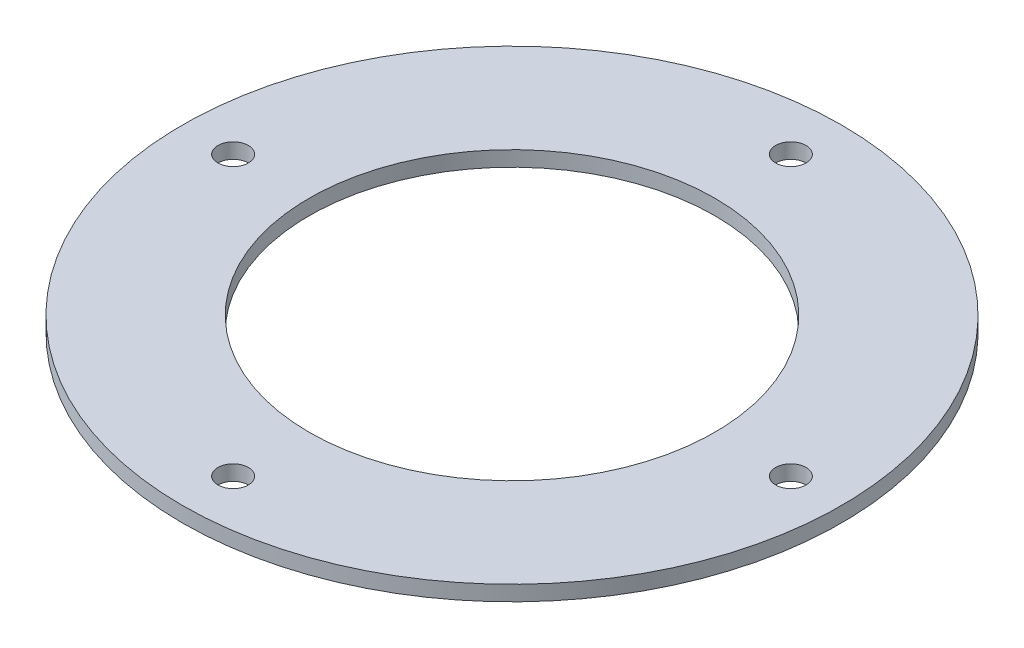
SolidWorks part; units mm, degrees
ref_plane "Front Plane" through (0, 0, 0) normal (0, 0, 1) x (1, 0, 0)
ref_plane "Top Plane" through (0, 0, 0) normal (0, 1, 0) x (1, 0, 0)
ref_plane "Right Plane" through (0, 0, 0) normal (1, 0, 0) x (0, 0, -1)
sketch "Sketch1" plane through (0, 0, 0) normal (0, 1, 0) x (1, 0, 0)
  circle A0 centre (0, 0) radius 65
  dimension "D1" = 130
extrude "Boss-Extrude1" add sketch "Sketch1" along normal blind 3
sketch "Sketch2" plane through (0, 3, 0) normal (0, 1, 0) x (1, 0, 0)
  circle A0 centre (0, 0) radius 55 construction
  circle A1 centre (0, 55) radius 3
  dimension "D1" = 110
  dimension "D2" = 6
extrude "Cut-Extrude1" cut sketch "Sketch2" against normal through all
pattern_circular "CirPattern1" count 4 over 360 about axis through (0, 0, 0) along (0, 1, 0) of "Cut-Extrude1"
sketch "Sketch3" plane through (0, 3, 0) normal (0, 1, 0) x (1, 0, 0)
  circle A0 centre (0, 0) radius 40
  dimension "D1" = 80
extrude "Cut-Extrude2" cut sketch "Sketch3" against normal through all
